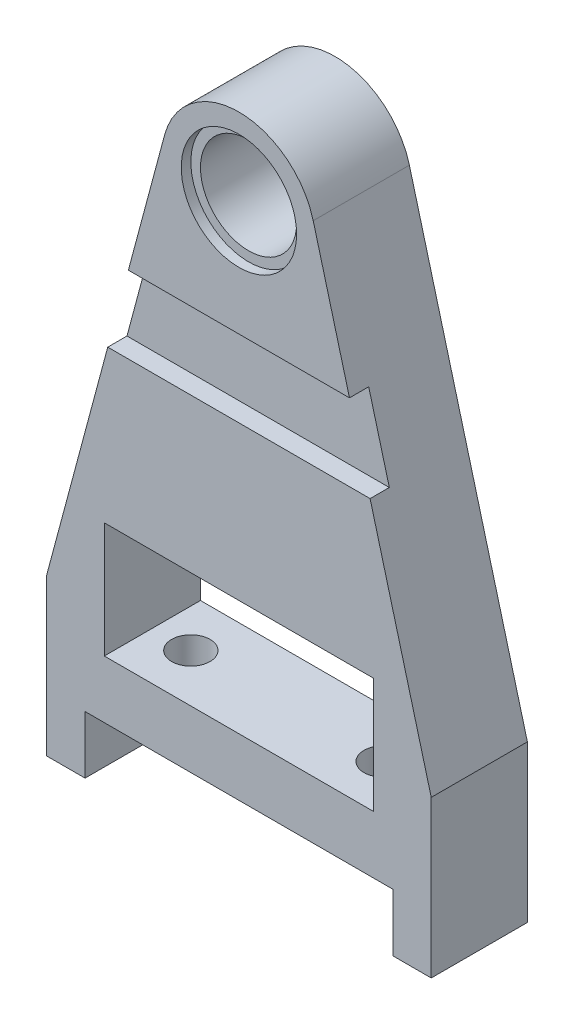
SolidWorks part; units mm, degrees
ref_plane "Front Plane" through (0, 0, 0) normal (0, 0, 1) x (1, 0, 0)
ref_plane "Top Plane" through (0, 0, 0) normal (0, 1, 0) x (1, 0, 0)
ref_plane "Right Plane" through (0, 0, 0) normal (1, 0, 0) x (0, 0, -1)
sketch "Sketch1" plane through (0, 0, 0) normal (0, 0, 1) x (1, 0, 0)
  line L0 (0, 0) -> (0, 300) construction
  line L5 (80, 30) -> (-80, 30)
  line L6 (-80, 30) -> (-80, 0)
  line L7 (-80, 0) -> (-100, 0)
  line L8 (-100, 0) -> (-100, 81.3431)
  line L9 (-100, 81.3431) -> (-38.637, 310.3528)
  line L10 (0, 300) -> (0, 340) construction
  line L11 (70, 60) -> (70, 120)
  line L12 (70, 60) -> (-70, 60)
  line L14 (70, 120) -> (-70, 120)
  line L15 (-70, 60) -> (-70, 120)
  line L16 (100, 81.3431) -> (38.637, 310.3528)
  line L17 (100, 0) -> (100, 81.3431)
  line L18 (80, 0) -> (100, 0)
  line L19 (80, 30) -> (80, 0)
  arc A0 (38.637, 310.3528) -> (-38.637, 310.3528) centre (0, 300) ccw
  circle A2 centre (0, 300) radius 25
  point P12 (0, 60)
  point P20 (0, 120)
  point P24 (0, 30)
  dimension "D9" = 40
  dimension "D10" = 50
  dimension "D1" = 200
  dimension "D2" = 20
  dimension "D3" = 30
  dimension "D4" = 140
  dimension "D5" = 60
  dimension "D6" = 60
  dimension "D7" = 195
  dimension "D8" = 300
extrude "Boss-Extrude1" add sketch "Sketch1" along normal mid plane 50 contours L16 A0 L9 L8 L7 L6 L5 L19 L18 L17 A2 L12 L15 L14 L11
sketch "Sketch4" plane through (0, 0, 25) normal (0, 0, 1) x (1, 0, 0)
  circle A0 centre (0, 300) radius 30
  dimension "D1" = 60
extrude "Cut-Extrude1" cut sketch "Sketch4" against normal blind 5
mirror "Mirror1" about plane through (0, 0, 0) normal (0, 0, 1) of "Cut-Extrude1"
sketch "Sketch5" plane through (0, 0, 25) normal (0, 0, 1) x (1, 0, 0)
  line L0 (-57.488, 240) -> (57.488, 240)
  line L1 (-100, 81.3431) -> (-38.637, 310.3528) construction
  line L2 (100, 81.3431) -> (38.637, 310.3528) construction
  line L3 (57.488, 240) -> (68.206, 200)
  line L4 (68.206, 200) -> (-68.206, 200)
  line L5 (-68.206, 200) -> (-57.488, 240)
  line L6 (-80, 0) -> (-100, 0) construction
  dimension "D1" = 40
  dimension "D2" = 200
extrude "Cut-Extrude2" cut sketch "Sketch5" against normal blind 10
sketch "Sketch6" plane through (0, 30, 0) normal (0, -1, 0) x (1, 0, 0)
  line L0 (-50, 0) -> (0, 0) construction
  line L1 (0, 0) -> (0, 25) construction
  line L2 (80, 25) -> (-80, 25) construction
  circle A0 centre (-50, 0) radius 10
  circle A1 centre (50, 0) radius 10
  dimension "D1" = 20
  dimension "D2" = 50
extrude "Cut-Extrude3" cut sketch "Sketch6" against normal up to next
